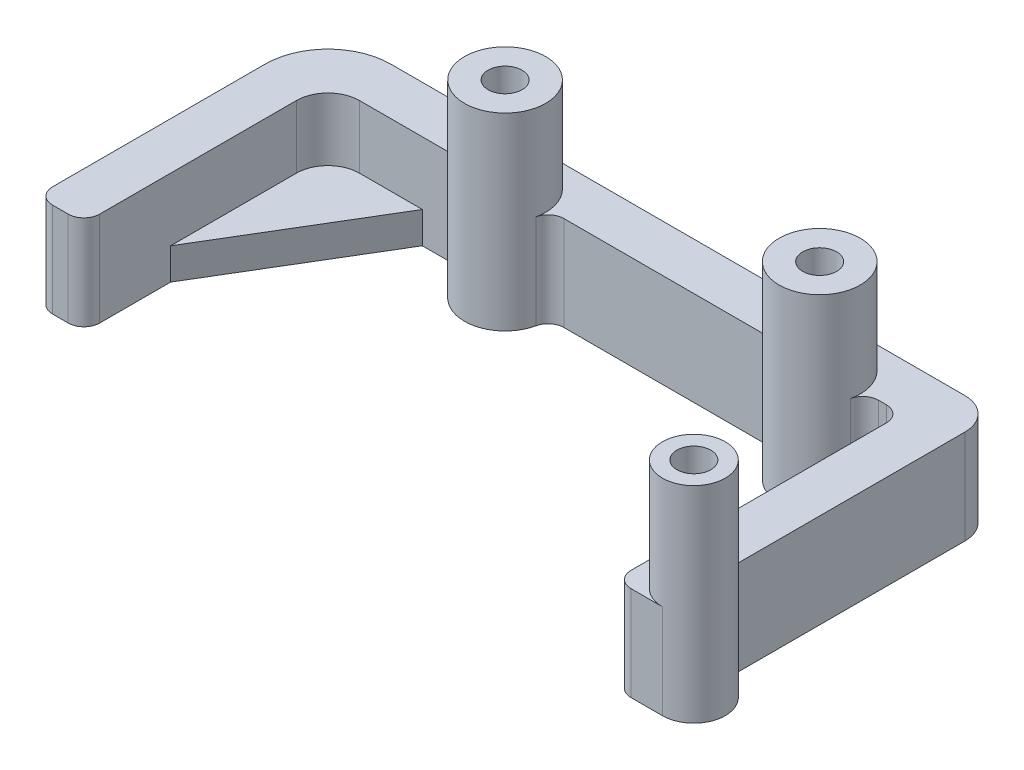
SolidWorks part; units mm, degrees
ref_plane "Front Plane" through (0, 0, 0) normal (0, 0, 1) x (1, 0, 0)
ref_plane "Top Plane" through (0, 0, 0) normal (0, 1, 0) x (1, 0, 0)
ref_plane "Right Plane" through (0, 0, 0) normal (1, 0, 0) x (0, 0, -1)
sketch "Sketch1" plane through (0, 0, 0) normal (0, 1, 0) x (-1, 0, 0)
  line L0 (0, 0) -> (141.2875, 0)
  line L2 (141.2875, 0) -> (141.2875, 65.1236)
  line L5 (0, 65.1236) -> (0, 0)
  line L6 (141.2875, 65.1236) -> (0, 65.1236)
  circle A0 centre (6.35, 16.6371) radius 2.667
  circle A9 centre (6.35, 42.0371) radius 2.667
  circle A10 centre (6.35, 67.4371) radius 2.667
  circle A11 centre (19.05, 16.6371) radius 2.667
  circle A12 centre (31.75, 16.6371) radius 2.667
  circle A13 centre (44.45, 16.6371) radius 2.667
  circle A14 centre (57.15, 16.6371) radius 2.667
  circle A15 centre (69.85, 16.6371) radius 2.667
  circle A16 centre (82.55, 16.6371) radius 2.667
  circle A17 centre (95.25, 16.6371) radius 2.667
  circle A18 centre (107.95, 16.6371) radius 2.667
  dimension "D1" = 5.334
  dimension "D4" = 25.4
  dimension "D5" = 25.4
  dimension "D6" = 9
  dimension "D7" = 12.7
  dimension "D2" = 65.1236
  dimension "D3" = 141.2875
  dimension "D8" = 6.35
  dimension "D9" = 16.6371
sketch "Sketch2" plane through (0, 0, 0) normal (0, 1, 0) x (1, 0, 0)
  line L1 (-141.2875, 0) -> (-141.2875, -65.1236) construction
  line L2 (-84.1426, -15.875) -> (-42.8574, -15.875)
  line L3 (-20.6426, -15.875) -> (-19.05, -15.875)
  line L4 (-6.35, -73.7871) -> (-12.7, -73.7871)
  line L19 (-141.2875, -19.05) -> (-141.2875, -61.9486)
  line L20 (-6.35, -6.35) -> (-141.2875, -6.35)
  line L21 (-6.35, -65.1236) -> (-6.35, -6.35)
  line L22 (-12.7, -6.35) -> (-128.5875, -6.35)
  line L23 (-6.35, -58.4568) -> (-6.35, -12.7)
  line L27 (-138.1125, -65.1236) -> (-134.9375, -65.1236)
  line L28 (-141.2875, -65.1236) -> (0, -65.1236) construction
  line L29 (-131.7625, -61.9486) -> (-131.7625, -22.225)
  line L30 (-125.4125, -15.875) -> (-106.3574, -15.875)
  line L31 (-15.875, -19.05) -> (-15.875, -70.6121)
  arc A4 (-6.35, -12.7) -> (-12.7, -6.35) centre (-12.7, -12.7) ccw
  circle A6 centre (-95.25, -16.6371) radius 3.429
  circle A7 centre (-31.75, -16.6371) radius 3.429
  arc A8 (-141.2875, -19.05) -> (-128.5875, -6.35) centre (-128.5875, -19.05) cw
  arc A12 (-134.9375, -65.1236) -> (-131.7625, -61.9486) centre (-134.9375, -61.9486) ccw
  arc A15 (-19.05, -15.875) -> (-15.875, -19.05) centre (-19.05, -19.05) cw
  arc A16 (-131.7625, -22.225) -> (-125.4125, -15.875) centre (-125.4125, -22.225) cw
  arc A17 (-138.1125, -65.1236) -> (-141.2875, -61.9486) centre (-138.1125, -61.9486) cw
  arc A18 (-103.2548, -18.376) -> (-87.2452, -18.376) centre (-95.25, -16.6371) ccw
  arc A19 (-39.7548, -18.376) -> (-23.7452, -18.376) centre (-31.75, -16.6371) ccw
  circle A20 centre (-95.25, -16.6371) radius 8.1915 construction
  circle A21 centre (-31.75, -16.6371) radius 8.1915 construction
  arc A22 (-103.2548, -18.376) -> (-106.3574, -15.875) centre (-106.3574, -19.05) ccw
  arc A23 (-87.2452, -18.376) -> (-84.1426, -15.875) centre (-84.1426, -19.05) cw
  arc A24 (-39.7548, -18.376) -> (-42.8574, -15.875) centre (-42.8574, -19.05) ccw
  arc A25 (-23.7452, -18.376) -> (-20.6426, -15.875) centre (-20.6426, -19.05) cw
  circle A27 centre (-6.35, -67.4371) radius 3.429
  arc A29 (-6.35, -73.7871) -> (-4.2333, -61.4502) centre (-6.35, -67.4371) ccw
  arc A30 (-6.35, -58.4568) -> (-4.2333, -61.4502) centre (-3.175, -58.4568) ccw
  arc A31 (-15.875, -70.6121) -> (-12.7, -73.7871) centre (-12.7, -70.6121) ccw
  point P30 (-141.2875, -6.35)
  point P31 (-141.2875, -65.1236)
  point P42 (-131.7625, -65.1236)
  point P44 (0, 0)
  point P48 (0, 0)
  point P53 (-87.094, -15.875)
  point P58 (-23.594, -15.875)
  point P62 (0, 0)
  point P64 (0, 0)
  dimension "D1" = 6.35
  dimension "D2" = 6.35
  dimension "D3" = 9.525
  dimension "D7" = 9.525
  dimension "D4" = 6.858
  dimension "D9" = 12.7
  dimension "D10" = 3.175
  dimension "D6" = 3.175
  dimension "D12" = 3.175
  dimension "D13" = 3.175
  dimension "D14" = 6.35
  dimension "D11" = 6.35
  dimension "D5" = 4.7625
  dimension "D8" = 9.525
extrude "Boss-Extrude1" add sketch "Sketch2" against normal blind 19.05
sketch "Sketch3" plane through (0, 0, 0) normal (0, 1, 0) x (1, 0, 0)
  circle A0 centre (-95.25, -16.6371) radius 8.1915
  circle A1 centre (-31.75, -16.6371) radius 8.1915
  circle A2 centre (-6.35, -67.4371) radius 6.35
  circle A3 centre (-95.25, -16.6371) radius 3.429
  circle A4 centre (-31.75, -16.6371) radius 3.429
  circle A5 centre (-6.35, -67.4371) radius 3.429
  arc A6 (-103.2548, -18.376) -> (-87.2452, -18.376) centre (-95.25, -16.6371) ccw construction
  arc A7 (-6.35, -73.7871) -> (-4.2333, -61.4502) centre (-6.35, -67.4371) ccw construction
  dimension "D2" = 6.858
extrude "Boss-Extrude2" add sketch "Sketch3" along normal blind 19.05
sketch "Sketch4" plane through (0, 19.05, 0) normal (0, 1, 0) x (1, 0, 0)
  circle A0 centre (-6.35, -67.4371) radius 3.429 construction
  circle A1 centre (-6.35, -67.4371) radius 6.35 construction
  circle A2 centre (-6.35, -67.4371) radius 3.429
  circle A3 centre (-6.35, -67.4371) radius 6.35
sketch "Sketch6" plane through (0, 0, 0) normal (0, 1, 0) x (1, 0, 0)
  line L0 (-112.7125, -15.875) -> (-131.7625, -47.625)
  line L2 (-131.7625, -47.625) -> (-131.7625, -15.875)
  line L3 (-131.7625, -15.875) -> (-112.7125, -15.875)
  line L5 (-84.1426, -15.875) -> (-42.8574, -15.875) construction
  line L6 (-131.7625, -61.9486) -> (-131.7625, -22.225) construction
  dimension "D1" = 19.05
  dimension "D2" = 31.75
extrude "Boss-Extrude5" add sketch "Sketch4" along normal blind 3.429
extrude "Boss-Extrude6" add sketch "Sketch6" along normal blind 6.35 from surface at -19.05 starting at face at (-31.75, -19.05, 20.0661)
equation "\"D3\"=1.58333"
